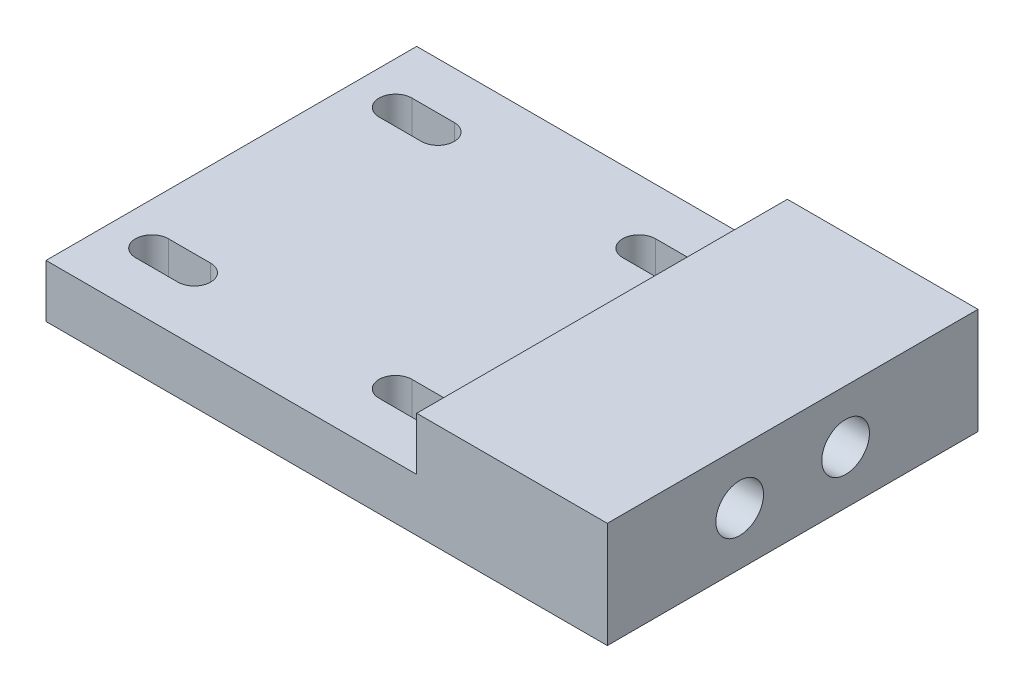
SolidWorks part; units mm, degrees
ref_plane "Front Plane" through (0, 0, 0) normal (0, 0, 1) x (1, 0, 0)
ref_plane "Top Plane" through (0, 0, 0) normal (0, 1, 0) x (1, 0, 0)
ref_plane "Right Plane" through (0, 0, 0) normal (1, 0, 0) x (0, 0, -1)
sketch "Sketch1" plane through (0, 0, 0) normal (0, 0, 1) x (1, 0, 0)
  line L0 (8.5, 5) -> (8.5, 0)
  line L1 (8.5, 5) -> (26.5, 5)
  line L2 (-26.5, 0) -> (-26.5, -5)
  line L3 (-26.5, -5) -> (26.5, -5)
  line L4 (26.5, 5) -> (26.5, -5)
  line L5 (-26.5, 5) -> (26.5, -5) construction
  line L6 (-26.5, -5) -> (26.5, 5) construction
  line L7 (8.5, 0) -> (-26.5, 0)
  line L8 (8.5, 0) -> (8.5, -5) construction
  line L9 (-26.5, -5) -> (-26.5, 5) construction
  line L10 (26.5, 5) -> (-26.5, 5) construction
  point P0 (0, 0)
  dimension "D1" = 10
  dimension "D2" = 35
  dimension "D3" = 18
extrude "Boss-Extrude1" add sketch "Sketch1" along normal blind 35
sketch "Sketch2" plane through (26.5, 0, 0) normal (1, 0, 0) x (0, 0, -1)
  line L0 (-35, 0) -> (0, 0) construction
  line L1 (-35, -5) -> (-35, 5) construction
  line L2 (-22.5, 2.25) -> (-35, 2.25) construction
  line L3 (-12.5, 2.25) -> (0, 2.25) construction
  line L4 (0, -5) -> (0, 5) construction
  line L5 (-17.5, 5) -> (-17.5, -5) construction
  line L6 (-35, 5) -> (0, 5) construction
  line L7 (-35, -5) -> (0, -5) construction
  line L8 (-22.5, 2.25) -> (-17.5, 2.25) construction
  line L9 (-12.5, -2.25) -> (-17.5, -2.25) construction
  circle A0 centre (-22.5, 0) radius 2.25
  circle A1 centre (-12.5, 0) radius 2.25
  dimension "D1" = 4.5
  dimension "D2" = 10
extrude "Cut-Extrude1" cut sketch "Sketch2" against normal blind 10
sketch "Sketch3" plane through (0, 0, 0) normal (0, 1, 0) x (1, 0, 0)
  line L0 (-20.5, 0) -> (-20.5, -35) construction
  line L1 (8.5, 0) -> (-26.5, 0) construction
  line L2 (8.5, -35) -> (-26.5, -35) construction
  line L3 (-20.5, -6) -> (-22.5, -6) construction
  line L4 (-26.5, -17.5) -> (-20.5, -17.5) construction
  line L5 (-26.5, -35) -> (-26.5, 0) construction
  line L6 (0.95, -17.5) -> (0.95, -6) construction
  line L7 (0.95, -29) -> (0.95, -17.5) construction
  line L8 (-18.5, -6) -> (-20.5, -6) construction
  line L9 (-18.95, -17.5) -> (-20.5, -17.5) construction
  line L10 (-22.5, -7.55) -> (-18.5, -7.55)
  line L11 (-22.5, -30.55) -> (-18.5, -30.55)
  line L12 (-22.5, -27.45) -> (-18.5, -27.45)
  line L13 (-18.5, -29) -> (-20.5, -29) construction
  line L14 (-20.5, -29) -> (-22.5, -29) construction
  line L15 (-22.5, -4.45) -> (-18.5, -4.45)
  line L16 (-18.95, -29) -> (-18.95, -17.5) construction
  line L17 (-18.95, -17.5) -> (-18.95, -6) construction
  line L18 (-9, -35) -> (-9, 0) construction
  line L19 (2.5, -29) -> (4.5, -29) construction
  line L20 (0.5, -29) -> (2.5, -29) construction
  line L21 (0.95, -17.5) -> (2.5, -17.5) construction
  line L22 (0.5, -6) -> (2.5, -6) construction
  line L23 (8.5, -17.5) -> (2.5, -17.5) construction
  line L24 (2.5, -6) -> (4.5, -6) construction
  line L25 (2.5, 0) -> (2.5, -35) construction
  line L26 (4.5, -4.45) -> (0.5, -4.45)
  line L27 (4.5, -27.45) -> (0.5, -27.45)
  line L28 (4.5, -30.55) -> (0.5, -30.55)
  line L29 (4.5, -7.55) -> (0.5, -7.55)
  line L30 (8.5, -35) -> (8.5, 0) construction
  circle A0 centre (-20.5, -6) radius 1.55 construction
  circle A1 centre (-20.5, -29) radius 1.55 construction
  arc A2 (-22.5, -4.45) -> (-22.5, -7.55) centre (-22.5, -6) ccw
  arc A3 (-18.5, -4.45) -> (-18.5, -7.55) centre (-18.5, -6) cw
  arc A4 (-18.5, -30.55) -> (-18.5, -27.45) centre (-18.5, -29) ccw
  arc A5 (-22.5, -30.55) -> (-22.5, -27.45) centre (-22.5, -29) cw
  circle A6 centre (2.5, -29) radius 1.55 construction
  circle A7 centre (2.5, -6) radius 1.55 construction
  arc A8 (4.5, -30.55) -> (4.5, -27.45) centre (4.5, -29) ccw
  arc A9 (0.5, -30.55) -> (0.5, -27.45) centre (0.5, -29) cw
  arc A10 (0.5, -4.45) -> (0.5, -7.55) centre (0.5, -6) ccw
  arc A11 (4.5, -4.45) -> (4.5, -7.55) centre (4.5, -6) cw
  dimension "D3" = 23
  dimension "D2" = 3.1
  dimension "D1" = 23
  dimension "D4" = 2
extrude "Cut-Extrude2" cut sketch "Sketch3" against normal up to surface (5 mm away) up to face at (0, -5, 17.5)
